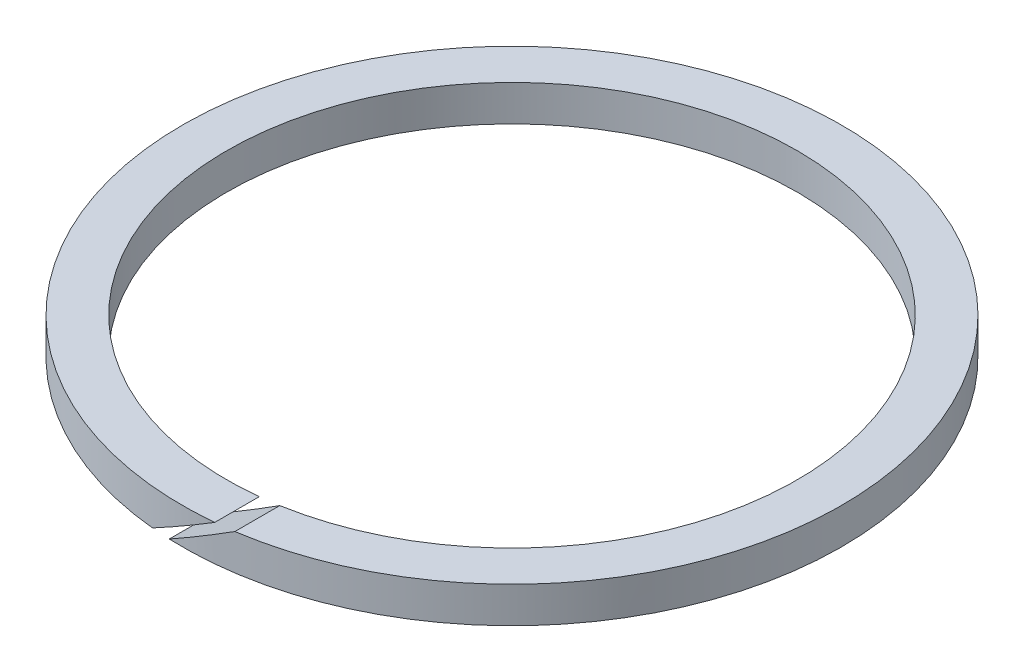
SolidWorks part; units mm, degrees
material "Gray Cast Iron"
ref_plane "Front Plane" through (0, 0, 0) normal (0, 0, 1) x (1, 0, 0)
ref_plane "Top Plane" through (0, 0, 0) normal (0, 1, 0) x (1, 0, 0)
ref_plane "Right Plane" through (0, 0, 0) normal (1, 0, 0) x (0, 0, -1)
sketch "Sketch1" plane through (0, 0, 0) normal (0, 1, 0) x (1, 0, 0)
  circle A0 centre (0, 0) radius 27.5
  circle A1 centre (0, 0) radius 23.8
  dimension "D1" = 55
  dimension "D2" = 47.6
extrude "Boss-Extrude1" add sketch "Sketch1" along normal blind 3
ref_plane "Plane1" through (0, 0, 27.5) normal (0, 0, 1) x (1, 0, 0)
sketch "Sketch2" plane through (0, 0, 27.5) normal (0, 0, 1) x (1, 0, 0)
  line L0 (-2.6278, 0) -> (2.5684, 3)
  line L1 (30.25, 0) -> (-30.25, 0) construction
  line L2 (27.5, 3) -> (-27.5, 3) construction
  line L3 (2.5684, 3) -> (4.0684, 3)
  line L4 (23.8, 3) -> (-23.8, 3) construction
  line L5 (4.0684, 3) -> (-1.1278, 0)
  line L6 (-1.1278, 0) -> (-2.6278, 0)
  line L7 (-8.6836, 0) -> (5.2279, 0) construction
  dimension "D1" = 1.5
  dimension "D2" = 30
extrude "Cut-Extrude1" cut sketch "Sketch2" against normal up to surface (3.7267 mm away)
